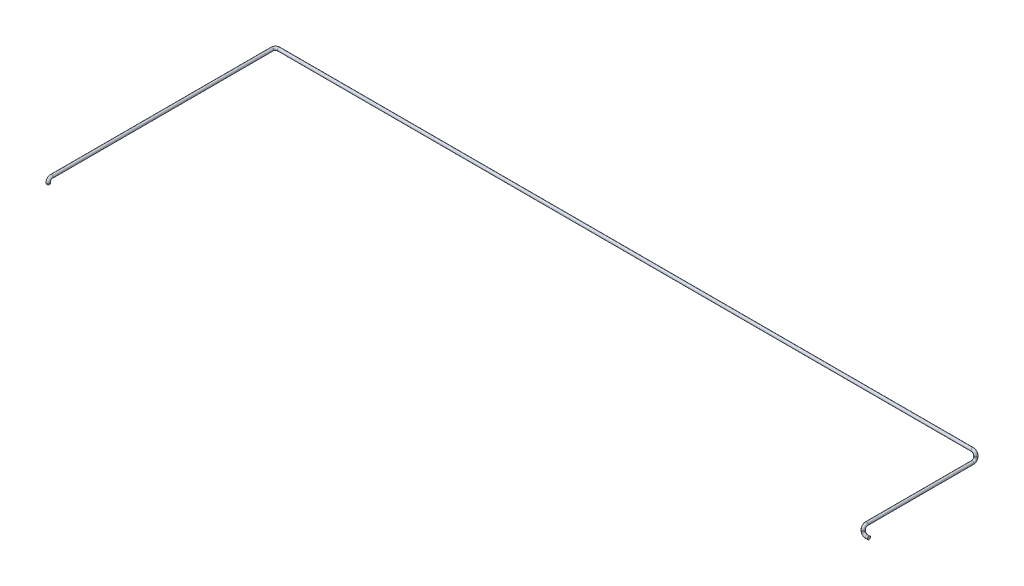
SolidWorks part; units mm, degrees
ref_plane "Alzado" through (0, 0, 0) normal (0, 0, 1) x (1, 0, 0)
ref_plane "Planta" through (0, 0, 0) normal (0, 1, 0) x (1, 0, 0)
ref_plane "Vista lateral" through (0, 0, 0) normal (1, 0, 0) x (0, 0, -1)
sketch3d "Croquis3D1"
  line L0 (0, 0, 0) -> (-20, 0, 0)
  line L1 (-50, 30, 0) -> (-50, 40, 0)
  line L2 (-50, 70, -30) -> (-50, 70, -970)
  line L6 (-50, 100, -1000) -> (-50, 110, -1000)
  line L7 (-80, 140, -1000) -> (-6245, 140, -1000)
  line L8 (-6275, 140, -970) -> (-6275, 140, 990)
  line L9 (-6275, 110, 1020) -> (-6275, 100, 1020)
  arc A0 (-6275, 140, 990) -> (-6275, 110, 1020) centre (-6275, 110, 990) ccw
  arc A1 (-6245, 140, -1000) -> (-6275, 140, -970) centre (-6245, 140, -970) ccw
  arc A2 (-50, 110, -1000) -> (-80, 140, -1000) centre (-80, 110, -1000) ccw
  arc A3 (-50, 100, -1000) -> (-50, 70, -970) centre (-50, 100, -970) ccw
  arc A4 (-50, 40, 0) -> (-50, 70, -30) centre (-50, 40, -30) ccw
  arc A5 (-20, 0, 0) -> (-50, 30, 0) centre (-20, 30, 0) ccw
  point P6 (-6275, 140, 1020)
  point P11 (-6245, 110, 990)
  point P15 (-6275, 140, -1000)
  point P16 (-6245, 170, -970)
  point P19 (-50, 140, -1000)
  point P20 (-80, 110, -970)
  point P23 (-50, 70, -1000)
  point P24 (-80, 100, -970)
  point P27 (-50, 70, 0)
  point P28 (-80, 40, -30)
  point P31 (-50, 0, 0)
  point P32 (-20, 30, -30)
  dimension "D8" = 30
  dimension "D1" = 50
  dimension "D2" = 70
  dimension "D3" = 1000
  dimension "D4" = 70
  dimension "D5" = 6225
  dimension "D6" = 2020
  dimension "D7" = 40
sketch "Croquis1" plane through (0, 0, 0) normal (1, 0, 0) x (0, 0, -1)
  circle A0 centre (0, 0) radius 13.7
  dimension "D1" = 27.4
sweep "Barrer1" add profiles "Croquis1" path "Croquis3D1"
